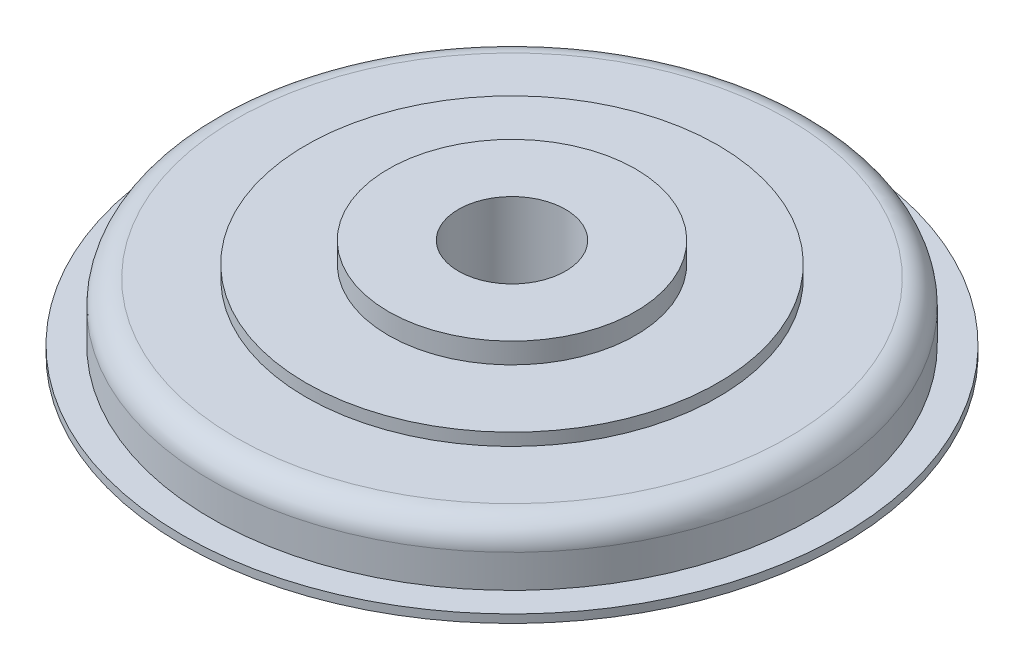
SolidWorks part; units mm, degrees
ref_plane "Front Plane" through (0, 0, 0) normal (0, 0, 1) x (1, 0, 0)
ref_plane "Top Plane" through (0, 0, 0) normal (0, 1, 0) x (1, 0, 0)
ref_plane "Right Plane" through (0, 0, 0) normal (1, 0, 0) x (0, 0, -1)
sketch "Sketch1" plane through (0, 0, 0) normal (0, 0, 1) x (1, 0, 0)
  line L0 (-200, -16.727) -> (-200, 108.0487) construction
  line L1 (-200, 0) -> (200, 0)
  line L3 (-200, 10) -> (200, 10)
  line L4 (200, 0) -> (200, 10)
  line L5 (0, 10) -> (165, 10)
  line L7 (-165, 35) -> (165, 35)
  line L8 (165, 10) -> (165, 35)
  line L9 (0, 35) -> (165, 35)
  line L11 (-135, 80) -> (135, 80)
  line L12 (165, 35) -> (165, 50)
  line L13 (-50, 80) -> (50, 80)
  line L15 (-50, 95) -> (50, 95)
  line L16 (50, 80) -> (50, 95)
  line L18 (-200, 0) -> (-200, 10)
  line L19 (-165, 10) -> (-165, 35)
  line L20 (-165, 35) -> (-165, 50)
  line L21 (-50, 80) -> (-50, 95)
  arc A0 (135, 80) -> (165, 50) centre (135, 50) cw
  arc A1 (-135, 80) -> (-165, 50) centre (-135, 50) ccw
revolve "Revolve2" add sketch "Sketch1" angle 360 about L0
sketch "Sketch4" plane through (0, 80, 0) normal (0, 1, 0) x (1, 0, 0)
  circle A0 centre (-200, 0) radius 65
  circle A1 centre (-200, 0) radius 150
extrude "Boss-Extrude3" add sketch "Sketch4" along normal blind 40
sketch "Sketch5" plane through (0, 10, 0) normal (0, 1, 0) x (1, 0, 0)
  circle A0 centre (-200, 0) radius 50
extrude "Cut-Extrude1" cut sketch "Sketch5" against normal through all
sketch "Sketch6" plane through (0, 120, 0) normal (0, 1, 0) x (1, 0, 0)
  circle A0 centre (-200, 0) radius 65
extrude "Cut-Extrude2" cut sketch "Sketch6" against normal through all
